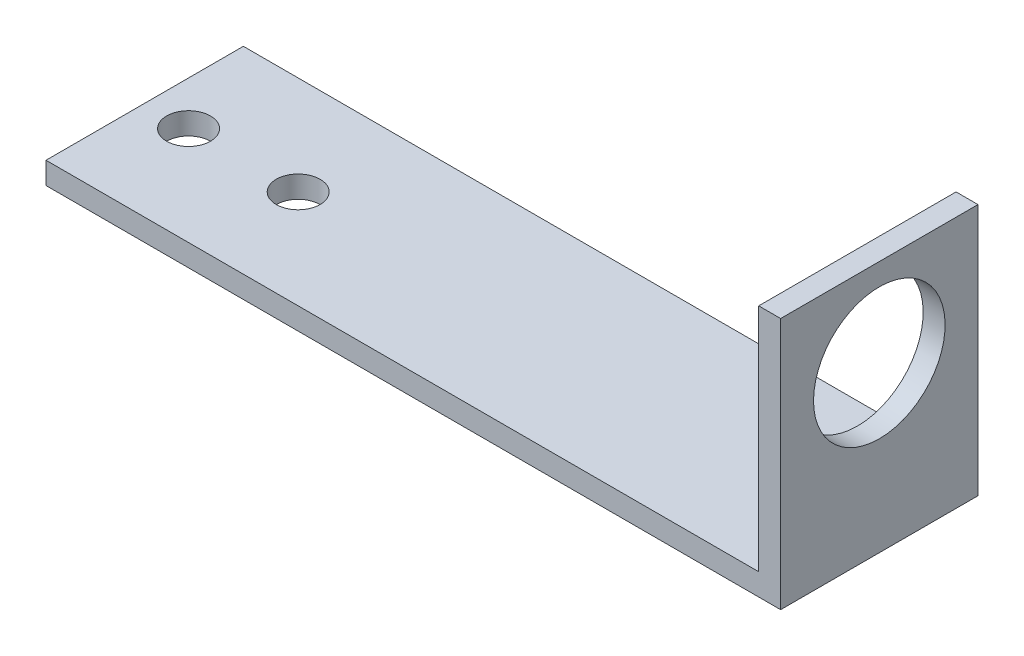
SolidWorks part; units mm, degrees
material "7075-T6 (SN)"
ref_plane "Front Plane" through (0, 0, 0) normal (0, 0, 1) x (1, 0, 0)
ref_plane "Top Plane" through (0, 0, 0) normal (0, 1, 0) x (1, 0, 0)
ref_plane "Right Plane" through (0, 0, 0) normal (1, 0, 0) x (0, 0, -1)
sketch "Sketch1" plane through (0, 0, 0) normal (0, 0, 1) x (1, 0, 0)
  line L0 (0, 0) -> (0, 23)
  line L1 (0, 23) -> (-2, 23)
  line L2 (-2, 23) -> (-2, 2)
  line L3 (-2, 2) -> (-67, 2)
  line L4 (-67, 2) -> (-67, 0)
  line L5 (-67, 0) -> (0, 0)
  dimension "D1" = 23
  dimension "D2" = 67
  dimension "D3" = 2
  dimension "D4" = 2
extrude "Boss-Extrude1" add sketch "Sketch1" along normal blind 18
sketch "Sketch2" plane through (-2, 0, 0) normal (-1, 0, 0) x (0, 0, 1)
  line L0 (9, 24.0134) -> (9, 6.2204) construction
  line L1 (18, 23) -> (0, 23) construction
  circle A0 centre (9, 15) radius 6
  point P4 (9, 23)
  dimension "D1" = 8
  dimension "D2" = 12
extrude "Cut-Extrude1" cut sketch "Sketch2" against normal up to next
sketch "Sketch3" plane through (0, 2, 0) normal (0, 1, 0) x (1, 0, 0)
  line L0 (-72.9806, -9) -> (-46.432, -9) construction
  line L1 (-67, -18) -> (-67, 0) construction
  circle A0 centre (-63, -9) radius 2
  circle A1 centre (-53, -9) radius 2
  point P4 (-67, -9)
  dimension "D1" = 4
  dimension "D2" = 10
  dimension "D3" = 4
  dimension "D4" = 4
extrude "Cut-Extrude2" cut sketch "Sketch3" against normal up to next
